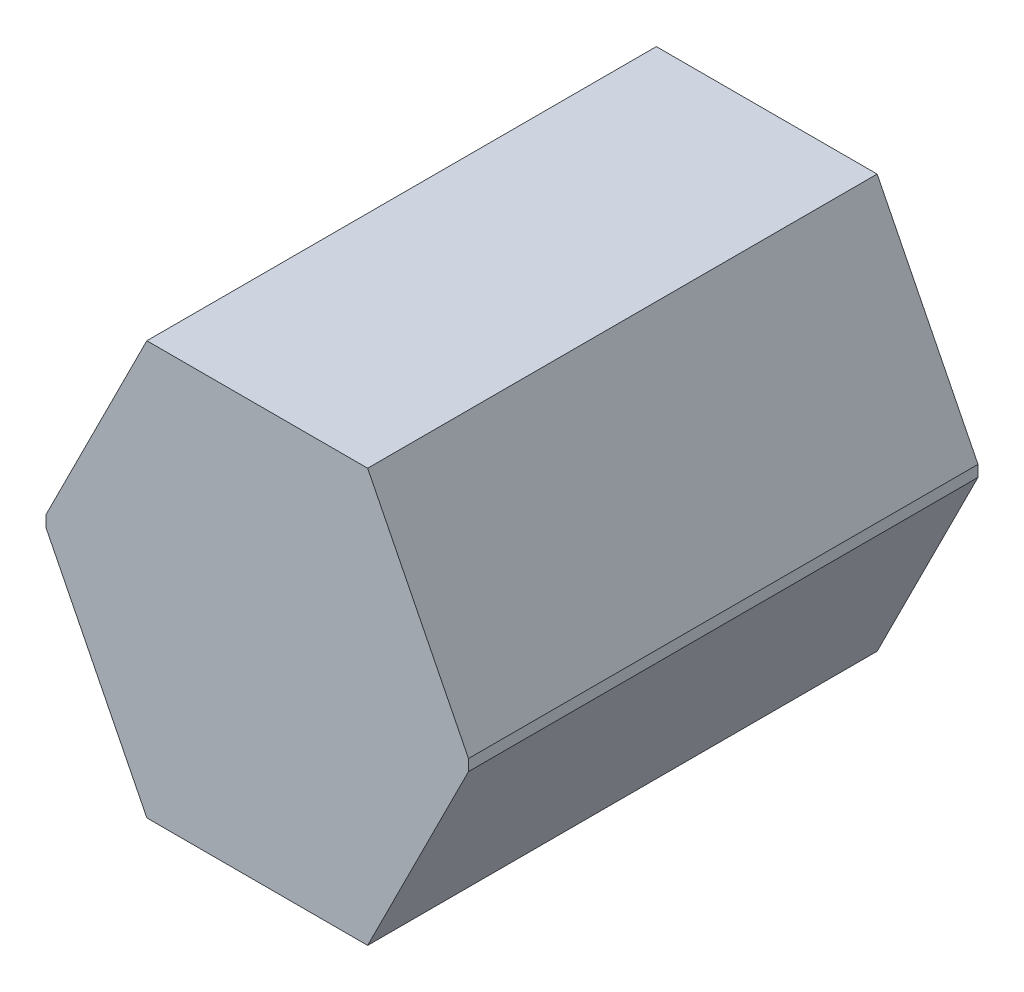
SolidWorks part; units mm, degrees
ref_plane "Ebene vorne" through (0, 0, 0) normal (0, 0, 1) x (1, 0, 0)
ref_plane "Ebene oben" through (0, 0, 0) normal (0, 1, 0) x (1, 0, 0)
ref_plane "Ebene rechts" through (0, 0, 0) normal (1, 0, 0) x (0, 0, -1)
sketch "Skizze1" plane through (0, 0, 0) normal (0, 0, 1) x (1, 0, 0)
  line L0 (0, 256.5451) -> (0, -264.2006) construction
  line L1 (298.5169, 0) -> (-248.6894, 0) construction
  line L2 (-97.5, 182.5) -> (97.5, 182.5)
  line L3 (-186.5786, 5) -> (-186.5786, -5)
  line L4 (-97.5, 182.5) -> (-186.5786, 5)
  line L5 (97.5, 182.5) -> (186.5786, 5)
  line L6 (186.5786, 5) -> (186.5786, -5)
  line L7 (97.5, -182.5) -> (186.5786, -5)
  line L8 (-97.5, -182.5) -> (-186.5786, -5)
  line L9 (-97.5, -182.5) -> (97.5, -182.5)
  point P7 (0, -182.5)
  point P12 (0, 182.5)
  point P14 (186.5786, 0)
  point P17 (-186.5786, 0)
  dimension "D1" = 365
  dimension "D2" = 338
  dimension "D3" = 195
  dimension "D4" = 10
extrude "Aufsatz-Linear austragen1" add sketch "Skizze1" along normal blind 450
